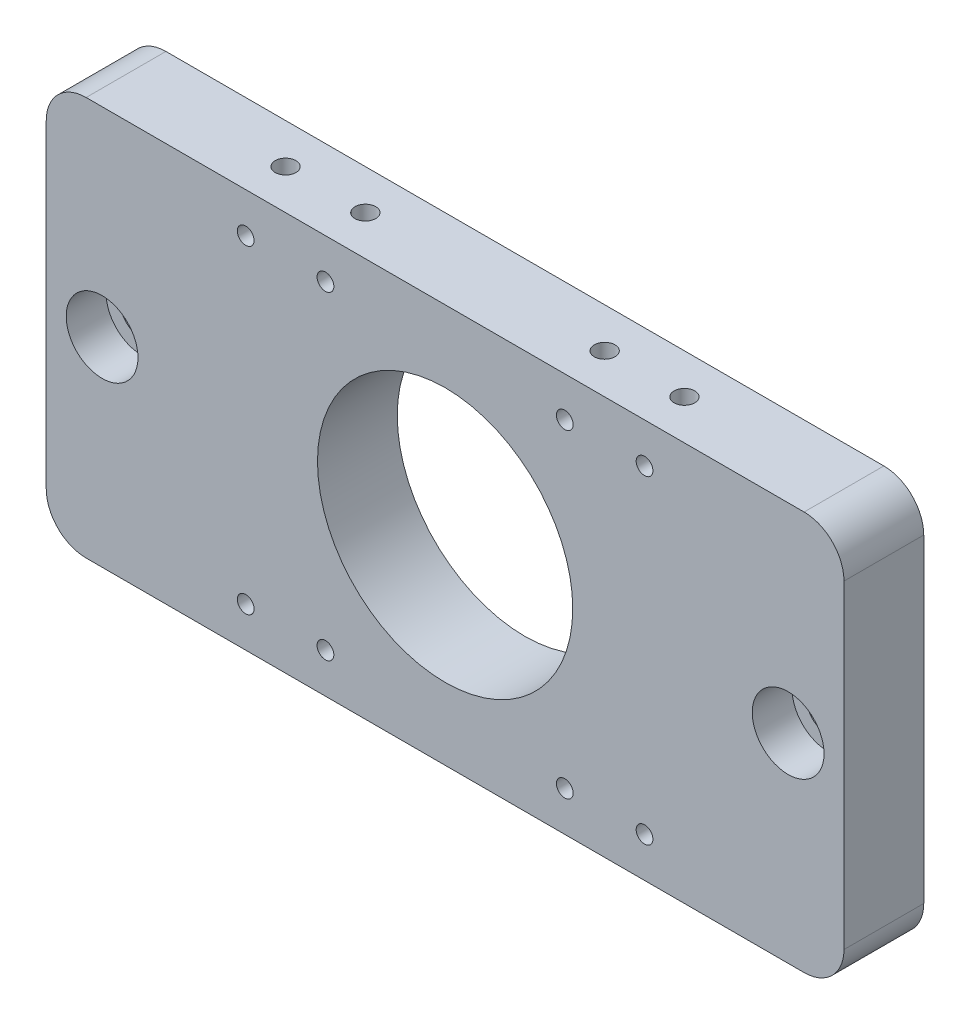
SolidWorks part; units mm, degrees
material "PTFE (general)"
ref_plane "Front Plane" through (0, 0, 0) normal (0, 0, 1) x (1, 0, 0)
ref_plane "Top Plane" through (0, 0, 0) normal (0, 1, 0) x (1, 0, 0)
ref_plane "Right Plane" through (0, 0, 0) normal (1, 0, 0) x (0, 0, -1)
sketch "Sketch1" plane through (0, 0, 0) normal (0, 0, 1) x (1, 0, 0)
  line L0 (0, 25) -> (100, 25) construction
  line L1 (0, 0) -> (100, 0)
  line L2 (0, 0) -> (0, 50)
  line L3 (0, 50) -> (100, 50)
  line L4 (100, 0) -> (100, 50)
  line L5 (50, 50) -> (50, 0) construction
  circle A0 centre (50, 25) radius 16
  circle A1 centre (7, 25) radius 2.75
  circle A2 centre (93, 25) radius 2.75
  dimension "D3" = 32
  dimension "D4" = 5.5
  dimension "D1" = 100
  dimension "D2" = 50
  dimension "D5" = 7
extrude "Boss-Extrude1" add sketch "Sketch1" along normal blind 10
sketch "Sketch2" plane through (0, 0, 10) normal (0, 0, 1) x (1, 0, 0)
  circle A0 centre (7, 25) radius 4.5
  circle A1 centre (93, 25) radius 4.5
  dimension "D1" = 9
extrude "Cut-Extrude1" cut sketch "Sketch2" against normal blind 5
sketch "Sketch3" plane through (0, 0, 10) normal (0, 0, 1) x (1, 0, 0)
  line L0 (0, 25) -> (100, 25) construction
  line L1 (0, 50) -> (0, 0) construction
  line L2 (100, 0) -> (100, 50) construction
  line L3 (50, 0) -> (50, 50) construction
  line L4 (0, 0) -> (100, 0) construction
  line L5 (100, 50) -> (0, 50) construction
  line L6 (0, 5) -> (100, 5) construction
  circle A0 centre (35, 5) radius 1.05
  circle A1 centre (25, 5) radius 1.05
  circle A2 centre (65, 5) radius 1.05
  circle A3 centre (75, 5) radius 1.05
  circle A4 centre (25, 45) radius 1.05
  circle A5 centre (35, 45) radius 1.05
  circle A6 centre (75, 45) radius 1.05
  circle A7 centre (65, 45) radius 1.05
  dimension "D2" = 2.1
  dimension "D1" = 5
  dimension "D3" = 15
  dimension "D4" = 10
extrude "Cut-Extrude2" cut sketch "Sketch3" against normal through all
sketch "Sketch4" plane through (0, 0, 0) normal (0, -1, 0) x (1, 0, 0)
  line L0 (0, 5) -> (100, 5) construction
  line L1 (0, 10) -> (0, 0) construction
  line L2 (100, 10) -> (100, 0) construction
  line L3 (50, 10) -> (50, 0) construction
  line L4 (0, 10) -> (100, 10) construction
  line L5 (0, 0) -> (100, 0) construction
  circle A0 centre (35, 5) radius 1.3
  circle A1 centre (25, 5) radius 1.3
  circle A2 centre (65, 5) radius 1.3
  circle A3 centre (75, 5) radius 1.3
  dimension "D3" = 2.6
  dimension "D1" = 15
  dimension "D2" = 10
extrude "Cut-Extrude3" cut sketch "Sketch4" against normal blind 10
ref_point "Point1"
ref_plane "Plane1" through (0, 25, 0) normal (0, 1, 0) x (1, 0, 0)
mirror "Mirror1" about plane through (0, 25, 0) normal (0, 1, 0) of "Cut-Extrude3"
fillet "Fillet1" radius 5 4 edges at (100, 50, 5) (100, 0, 5) (0, 0, 5) (0, 50, 5)
